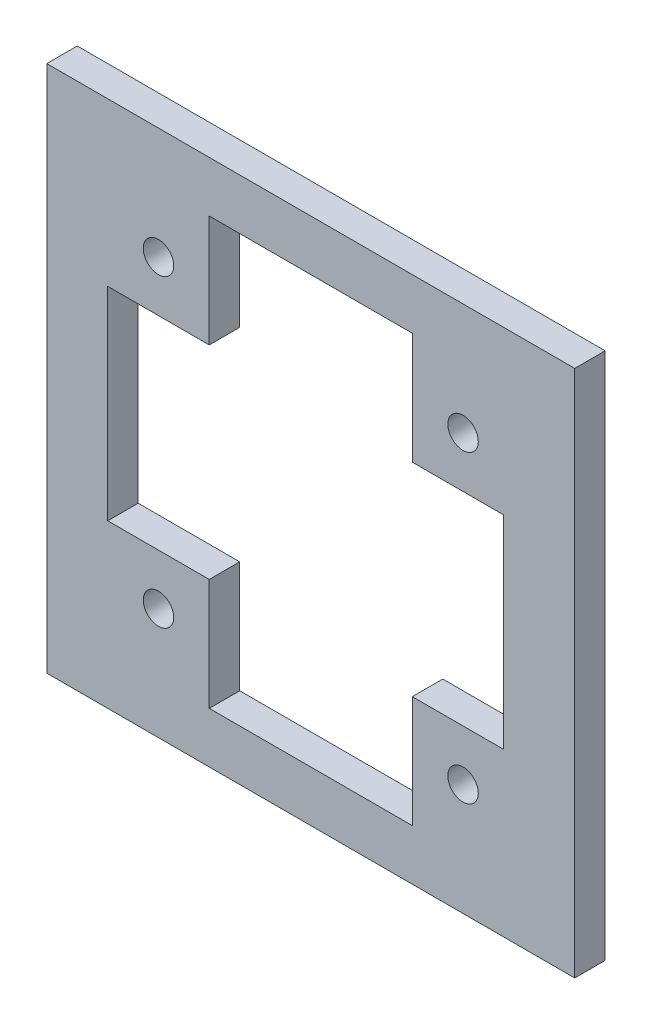
SolidWorks part; units mm, degrees
material "Resina de poliéster"
ref_plane "Alzado" through (0, 0, 0) normal (0, 0, 1) x (1, 0, 0)
ref_plane "Planta" through (0, 0, 0) normal (0, 1, 0) x (1, 0, 0)
ref_plane "Vista lateral" through (0, 0, 0) normal (1, 0, 0) x (0, 0, -1)
sketch "Model" plane through (0, 0, 0) normal (0, 0, 1) x (1, 0, 0)
  line L81 (52, 0) -> (52, 52)
  line L82 (0, 52) -> (0, 0)
  line L83 (0, 52) -> (0, 0)
  line L84 (0, 52) -> (52, 52)
  line L85 (52, 52) -> (52, 0)
  line L86 (0, 0) -> (52, 0)
  line L99 (11, 42.5) -> (11, 39.5)
  line L100 (9.5, 41) -> (12.5, 41)
  line L101 (39.5, 11) -> (42.5, 11)
  line L102 (41, 9.5) -> (41, 12.5)
  line L103 (11, 12.5) -> (11, 9.5)
  line L104 (9.5, 11) -> (12.5, 11)
  line L105 (41, 42.5) -> (41, 39.5)
  line L106 (39.5, 41) -> (42.5, 41)
  line L249 (6, 36) -> (6, 16)
  line L250 (16, 47) -> (16, 36)
  line L251 (6, 36) -> (16, 36)
  line L252 (6, 16) -> (16, 16)
  line L253 (16, 16) -> (16, 5)
  line L254 (16, 47) -> (36, 47)
  line L255 (45, 16) -> (45, 36)
  line L256 (36, 47) -> (36, 36)
  line L257 (36, 36) -> (45, 36)
  line L258 (36, 16) -> (45, 16)
  line L259 (16, 5) -> (36, 5)
  line L260 (36, 16) -> (36, 5)
  line L273 (3, 52) -> (3, 0) construction
  line L274 (48, 0) -> (48, 52) construction
  line L275 (45, 0) -> (45, 52) construction
  circle A112 centre (11, 41) radius 1.5
  circle A113 centre (11, 11) radius 1.5
  circle A114 centre (41, 11) radius 1.5
  circle A115 centre (41, 41) radius 1.5
  point P686 (11, 9.5)
  point P687 (11, 0)
  dimension "D9" = 52
  dimension "D10" = 52
  dimension "D11" = 4
  dimension "D12" = 11
  dimension "D13" = 11
extrude "Saliente-Extruir1" add sketch "Model" along normal blind 3 contours L82 L86 L81 L84 A115 A114 A113 A112 L258 L260 L259 L253 L252 L249 L251 L250 L254 L256 L257 L255
